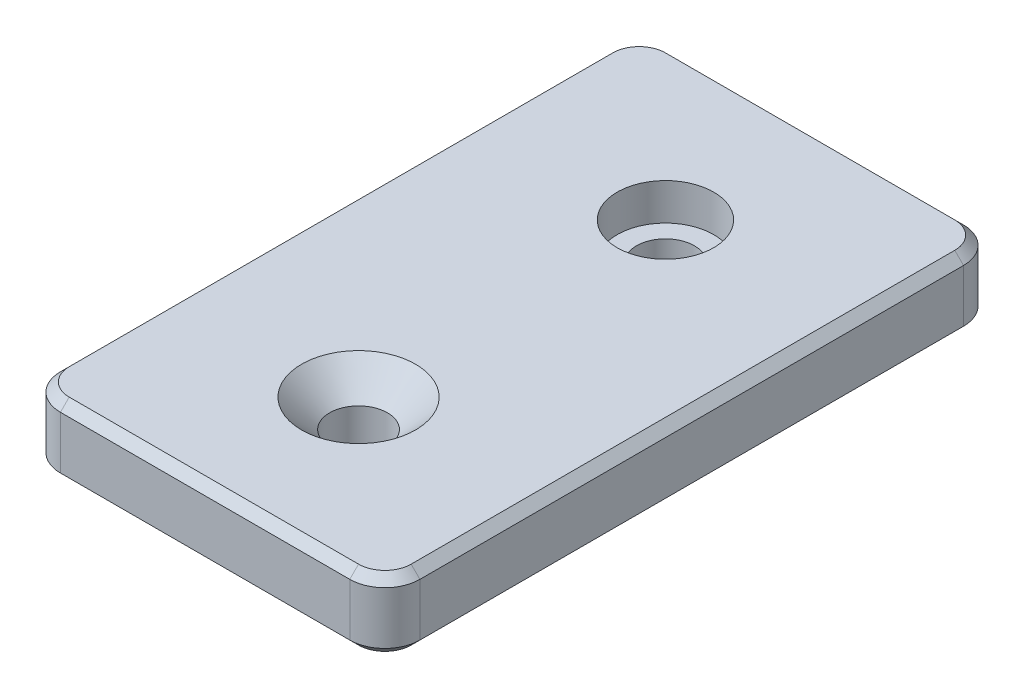
SolidWorks part; units mm, degrees
ref_plane "Front Plane" through (0, 0, 0) normal (0, 0, 1) x (1, 0, 0)
ref_plane "Top Plane" through (0, 0, 0) normal (0, 1, 0) x (1, 0, 0)
ref_plane "Right Plane" through (0, 0, 0) normal (1, 0, 0) x (0, 0, -1)
sketch "Sketch1" plane through (0, 0, 0) normal (0, 1, 0) x (1, 0, 0)
  line L1 (-20.5, 35) -> (20.5, 35)
  line L2 (-20.5, 35) -> (-20.5, -35)
  line L3 (-20.5, -35) -> (20.5, -35)
  line L4 (20.5, 35) -> (20.5, -35)
  line L5 (-20.5, 35) -> (20.5, -35) construction
  line L6 (-20.5, -35) -> (20.5, 35) construction
  point P0 (0, 0)
  dimension "D1" = 70
  dimension "D2" = 41
extrude "Boss-Extrude1" add sketch "Sketch1" along normal blind 8
fillet "Fillet1" radius 4 4 edges at (-20.5, 4, -35) (20.5, 4, -35) (20.5, 4, 35) (-20.5, 4, 35)
chamfer "Chamfer1" distance 1 angle 45 16 edges at (0, 0, 35) (19.3284, 0, 33.8284) (20.5, 0, 0) (19.3284, 0, -33.8284) (0, 0, -35) (-19.3284, 0, -33.8284) (-20.5, 0, 0) (-19.3284, 0, 33.8284) (19.3284, 8, 33.8284) (20.5, 8, 0) (19.3284, 8, -33.8284) (0, 8, -35) (-19.3284, 8, -33.8284) (-20.5, 8, 0) (-19.3284, 8, 33.8284) (0, 8, 35)
sketch "Sketch2" plane through (0, 8, 0) normal (0, 1, 0) x (1, 0, 0)
  line L0 (16.5, -35) -> (-16.5, -35) construction
  line L1 (-16.5, 35) -> (16.5, 35) construction
  circle A0 centre (0, -17.5) radius 3.3
  circle A1 centre (0, 17.5) radius 3.3
  dimension "D1" = 17.5
  dimension "D2" = 17.5
extrude "Cut-Extrude1" cut sketch "Sketch2" against normal blind 8
chamfer "Chamfer2" distance 3.2 angle 45 1 edges at (0, 8, 20.8)
sketch "Sketch3" plane through (0, 8, 0) normal (0, 1, 0) x (1, 0, 0)
  circle A0 centre (0, 17.5) radius 5.5
extrude "Cut-Extrude2" cut sketch "Sketch3" against normal blind 4.2
sketch "Sketch4" plane through (0, 8, 0) normal (0, 1, 0) x (1, 0, 0)
  circle A0 centre (0, 0) radius 5.1
extrude "Cut-Extrude3" cut sketch "Sketch4" against normal blind 10
sketch "Sketch5" plane through (0, 8, 0) normal (0, 1, 0) x (1, 0, 0)
  circle A0 centre (0, 0) radius 10
extrude "Cut-Extrude5" cut sketch "Sketch5" against normal blind 4
sketch "Sketch6" plane through (0, 8, 0) normal (0, 1, 0) x (1, 0, 0)
  circle A0 centre (0, 0) radius 10
extrude "Boss-Extrude2" add sketch "Sketch6" against normal up to surface (8 mm away) up to face at (0, 0, 5.1)
